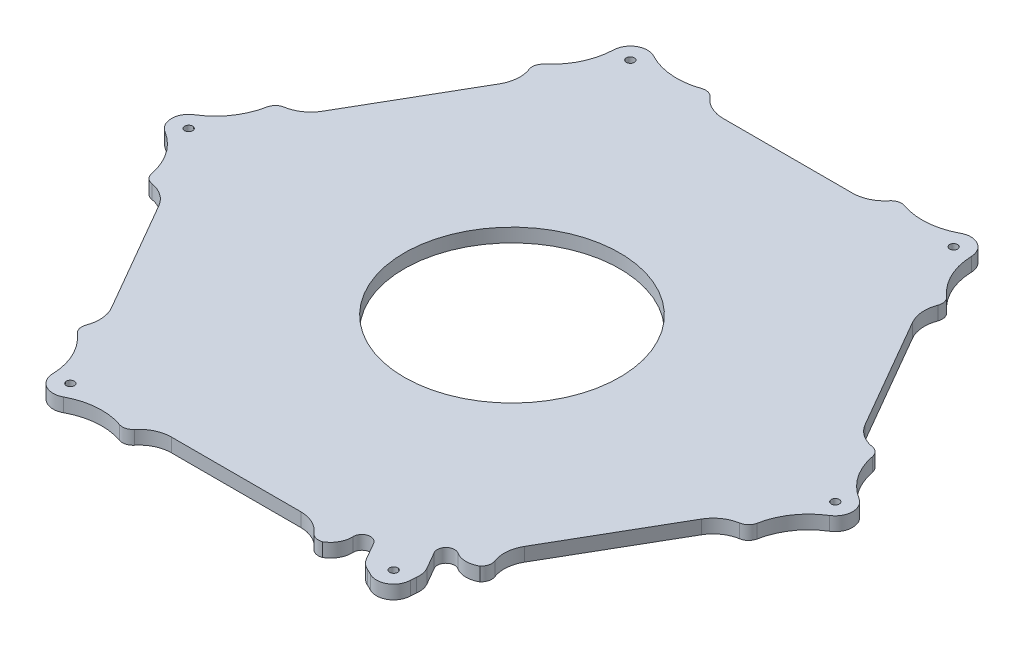
SolidWorks part; units mm, degrees
ref_plane "Front Plane" through (0, 0, 0) normal (0, 0, 1) x (1, 0, 0)
ref_plane "Top Plane" through (0, 0, 0) normal (0, 1, 0) x (1, 0, 0)
ref_plane "Right Plane" through (0, 0, 0) normal (1, 0, 0) x (0, 0, -1)
sketch "Sketch1" plane through (0, 0, 0) normal (0, 1, 0) x (1, 0, 0)
  line L0 (77.5674, -113.7749) -> (81.8959, -121.297)
  line L1 (81.8959, -121.297) -> (81.9043, -121.3116)
  line L2 (64.1068, -131.587) -> (64.1012, -131.5774)
  line L3 (64.1012, -131.5774) -> (59.6012, -123.7832)
  line L4 (30, -128) -> (-30, -128)
  line L5 (-95.8513, -89.9808) -> (-125.8513, -38.0192)
  line L6 (-125.8513, 38.0192) -> (-95.8513, 89.9808)
  line L7 (-30, 128) -> (30, 128)
  line L8 (95.8513, 89.9808) -> (125.8513, 38.0192)
  line L9 (125.8513, -38.0192) -> (95.8513, -89.9808)
  circle A0 centre (-75, -129.9038) radius 1.85
  circle A1 centre (75, -129.9038) radius 1.85
  circle A2 centre (150, 0) radius 1.85
  circle A3 centre (75, 129.9038) radius 1.85
  circle A4 centre (-75, 129.9038) radius 1.85
  circle A5 centre (-150, 0) radius 1.85
  circle A6 centre (0, 0) radius 50
  arc A7 (83.1894, -127.5042) -> (81.9043, -121.3116) centre (73.258, -126.3356) ccw
  arc A8 (83.1894, -127.5042) -> (82.9966, -130.1367) centre (112.9839, -131.0101) ccw
  arc A9 (71.2034, -136.9455) -> (82.9966, -130.1367) centre (75, -129.9038) ccw
  arc A10 (64.1068, -131.587) -> (68.8272, -135.7963) centre (72.7808, -126.6111) ccw
  arc A11 (59.6012, -123.7832) -> (52.1402, -125.94) centre (56.1371, -125.7832) ccw
  arc A12 (47.0958, -135.0222) -> (52.1402, -125.94) centre (42.1479, -126.332) ccw
  arc A13 (41.588, -133.4754) -> (47.0958, -135.0222) centre (45.4507, -130.3006) ccw
  arc A14 (41.588, -133.4754) -> (30, -128) centre (30, -143) ccw
  arc A15 (-30, -128) -> (-41.588, -133.4754) centre (-30, -143) ccw
  arc A16 (-47.0958, -135.0222) -> (-41.588, -133.4754) centre (-45.4507, -130.3006) ccw
  arc A17 (-47.0958, -135.0222) -> (-71.2034, -136.9455) centre (-56.9661, -163.352) ccw
  arc A18 (-82.9966, -130.1367) -> (-71.2034, -136.9455) centre (-75, -129.9038) ccw
  arc A19 (-82.9966, -130.1367) -> (-93.3848, -108.2972) centre (-112.9839, -131.0101) ccw
  arc A20 (-94.7991, -102.754) -> (-93.3848, -108.2972) centre (-90.1182, -104.5117) ccw
  arc A21 (-94.7991, -102.754) -> (-95.8513, -89.9808) centre (-108.8416, -97.4808) ccw
  arc A22 (-125.8513, -38.0192) -> (-136.3871, -30.7214) centre (-138.8416, -45.5192) ccw
  arc A23 (-140.4805, -26.725) -> (-136.3871, -30.7214) centre (-135.5689, -25.7888) ccw
  arc A24 (-140.4805, -26.725) -> (-154.2, -6.8088) centre (-169.95, -32.3419) ccw
  arc A25 (-154.2, 6.8088) -> (-154.2, -6.8088) centre (-150, 0) ccw
  arc A26 (-154.2, 6.8088) -> (-140.4805, 26.725) centre (-169.95, 32.3419) ccw
  arc A27 (-136.3871, 30.7214) -> (-140.4805, 26.725) centre (-135.5689, 25.7888) ccw
  arc A28 (-136.3871, 30.7214) -> (-125.8513, 38.0192) centre (-138.8416, 45.5192) ccw
  arc A29 (-95.8513, 89.9808) -> (-94.7991, 102.754) centre (-108.8416, 97.4808) ccw
  arc A30 (-93.3848, 108.2972) -> (-94.7991, 102.754) centre (-90.1182, 104.5117) ccw
  arc A31 (-93.3848, 108.2972) -> (-82.9966, 130.1367) centre (-112.9839, 131.0101) ccw
  arc A32 (-71.2034, 136.9455) -> (-82.9966, 130.1367) centre (-75, 129.9038) ccw
  arc A33 (-71.2034, 136.9455) -> (-47.0958, 135.0222) centre (-56.9661, 163.352) ccw
  arc A34 (-41.588, 133.4754) -> (-47.0958, 135.0222) centre (-45.4507, 130.3006) ccw
  arc A35 (-41.588, 133.4754) -> (-30, 128) centre (-30, 143) ccw
  arc A36 (30, 128) -> (41.588, 133.4754) centre (30, 143) ccw
  arc A37 (47.0958, 135.0222) -> (41.588, 133.4754) centre (45.4507, 130.3006) ccw
  arc A38 (47.0958, 135.0222) -> (71.2034, 136.9455) centre (56.9661, 163.352) ccw
  arc A39 (82.9966, 130.1367) -> (71.2034, 136.9455) centre (75, 129.9038) ccw
  arc A40 (82.9966, 130.1367) -> (93.3848, 108.2972) centre (112.9839, 131.0101) ccw
  arc A41 (94.7991, 102.754) -> (93.3848, 108.2972) centre (90.1182, 104.5117) ccw
  arc A42 (94.7991, 102.754) -> (95.8513, 89.9808) centre (108.8416, 97.4808) ccw
  arc A43 (125.8513, 38.0192) -> (136.3871, 30.7214) centre (138.8416, 45.5192) ccw
  arc A44 (140.4805, 26.725) -> (136.3871, 30.7214) centre (135.5689, 25.7888) ccw
  arc A45 (140.4805, 26.725) -> (154.2, 6.8088) centre (169.95, 32.3419) ccw
  arc A46 (154.2, -6.8088) -> (154.2, 6.8088) centre (150, 0) ccw
  arc A47 (154.2, -6.8088) -> (140.4805, -26.725) centre (169.95, -32.3419) ccw
  arc A48 (136.3871, -30.7214) -> (140.4805, -26.725) centre (135.5689, -25.7888) ccw
  arc A49 (136.3871, -30.7214) -> (125.8513, -38.0192) centre (138.8416, -45.5192) ccw
  arc A50 (95.8513, -89.9808) -> (94.7991, -102.754) centre (108.8416, -97.4808) ccw
  arc A51 (93.3848, -108.2972) -> (94.7991, -102.754) centre (90.1182, -104.5117) ccw
  arc A52 (82.9971, -108.1247) -> (93.3848, -108.2972) centre (88.3328, -99.6672) ccw
  arc A53 (82.9971, -108.1247) -> (77.5674, -113.7749) centre (80.8629, -111.5078) ccw
  arc A54 (71.2034, -136.9455) -> (68.8272, -135.7963) centre (56.9661, -163.352) ccw
extrude "Boss-Extrude1" add sketch "Sketch1" along normal blind 6.35
